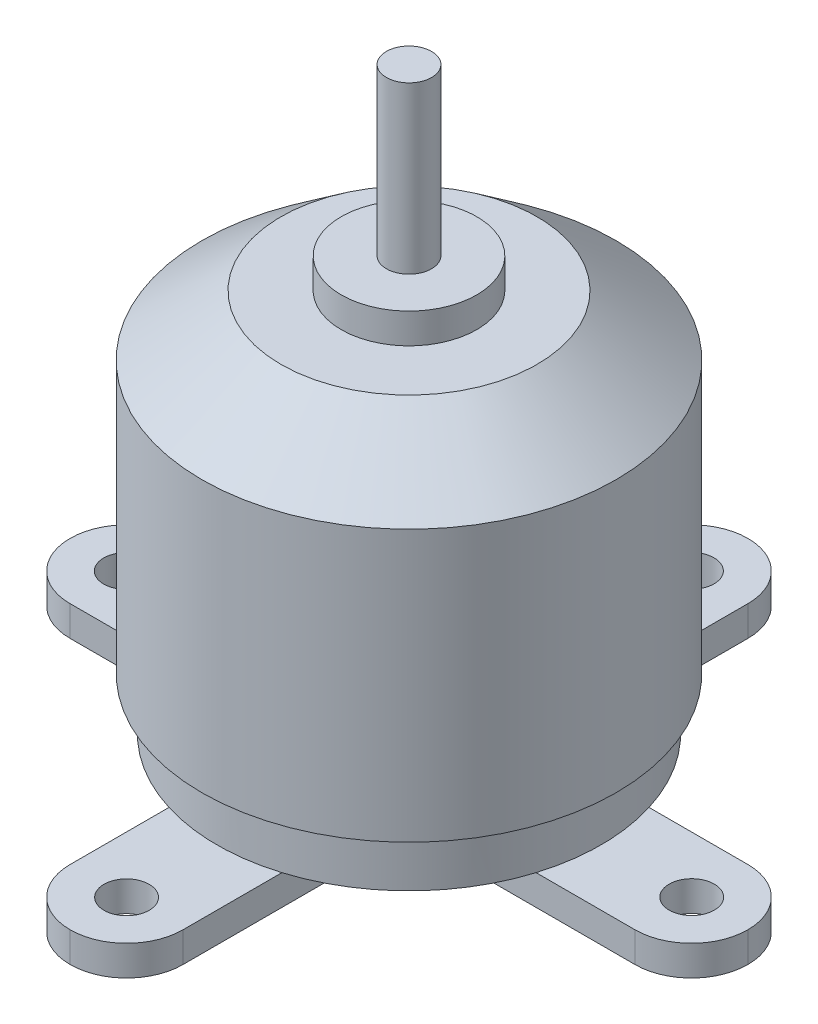
SolidWorks part; units mm, degrees
ref_plane "Alzado" through (0, 0, 0) normal (0, 0, 1) x (1, 0, 0)
ref_plane "Planta" through (0, 0, 0) normal (0, 1, 0) x (1, 0, 0)
ref_plane "Vista lateral" through (0, 0, 0) normal (1, 0, 0) x (0, 0, -1)
sketch "Croquis1" plane through (0, 0, 0) normal (0, 1, 0) x (1, 0, 0)
  circle A0 centre (0, 0) radius 13.75
  dimension "D1" = 27.5
extrude "Saliente-Extruir1" add sketch "Croquis1" along normal blind 18
sketch "Croquis3" plane through (0, 18, 0) normal (0, 1, 0) x (1, 0, 0)
  circle A0 centre (0, 0) radius 8.5
  dimension "D1" = 17
extrude "Saliente-Extruir2" add sketch "Croquis3" along normal blind 4
sketch "Croquis4" plane through (0, 22, 0) normal (0, 1, 0) x (1, 0, 0)
  circle A0 centre (0, 0) radius 4.5
  dimension "D1" = 9
extrude "Saliente-Extruir3" add sketch "Croquis4" along normal blind 2
sketch "Croquis5" plane through (0, 24, 0) normal (0, 1, 0) x (1, 0, 0)
  circle A0 centre (0, 0) radius 1.5
  dimension "D1" = 3
extrude "Saliente-Extruir4" add sketch "Croquis5" along normal blind 11
sketch "Croquis6" plane through (0, 0, 0) normal (0, 0, 1) x (1, 0, 0)
  line L0 (13.75, 18) -> (8.5, 22)
  line L1 (8.5, 22) -> (8.5, 18)
  line L2 (8.5, 18) -> (13.75, 18)
  line L3 (0, 18) -> (0, 0) construction
  line L4 (13.75, 18) -> (-13.75, 18) construction
revolve "Revolución1" add sketch "Croquis6" angle 360 about L3
sketch "Croquis7" plane through (0, 0, 0) normal (0, -1, 0) x (1, 0, 0)
  circle A0 centre (0, 0) radius 12.75
  dimension "D1" = 25.5
extrude "Saliente-Extruir5" add sketch "Croquis7" along normal blind 3.5
sketch "Croquis8" plane through (0, -3.5, 0) normal (0, -1, 0) x (1, 0, 0)
  line L0 (0, 18.9574) -> (0, -20.225) construction
  line L1 (0, 0) -> (-17.7259, 0) construction
  line L2 (7.49, 3.75) -> (18.76, 3.75)
  line L3 (0.01, 22.5) -> (-0.01, 22.5)
  line L4 (3.75, 18.76) -> (3.75, 7.49)
  line L5 (0.01, -22.5) -> (-0.01, -22.5)
  line L6 (-3.75, 18.76) -> (-3.75, 7.49)
  line L7 (3.75, 22.5) -> (-3.75, -22.5) construction
  line L8 (3.75, -22.5) -> (-3.75, 22.5) construction
  line L9 (-18.76, 3.75) -> (-7.49, 3.75)
  line L10 (-22.5, 0.01) -> (-22.5, -0.01)
  line L11 (-18.76, -3.75) -> (-7.49, -3.75)
  line L12 (22.5, 0.01) -> (22.5, -0.01)
  line L13 (-22.5, 3.75) -> (22.5, -3.75) construction
  line L14 (-22.5, -3.75) -> (22.5, 3.75) construction
  line L15 (3.75, -7.49) -> (3.75, -18.76)
  line L16 (7.49, -3.75) -> (18.76, -3.75)
  line L17 (-3.75, -7.49) -> (-3.75, -18.76)
  circle A0 centre (0, 0) radius 5
  arc A1 (3.75, -7.49) -> (7.49, -3.75) centre (7.49, -7.49) cw
  arc A2 (7.49, 3.75) -> (3.75, 7.49) centre (7.49, 7.49) cw
  arc A3 (-7.49, 3.75) -> (-3.75, 7.49) centre (-7.49, 7.49) ccw
  arc A4 (-7.49, -3.75) -> (-3.75, -7.49) centre (-7.49, -7.49) cw
  arc A5 (-22.5, -0.01) -> (-18.76, -3.75) centre (-18.76, -0.01) ccw
  arc A6 (-18.76, 3.75) -> (-22.5, 0.01) centre (-18.76, 0.01) ccw
  arc A7 (3.75, -18.76) -> (0.01, -22.5) centre (0.01, -18.76) cw
  arc A8 (-0.01, -22.5) -> (-3.75, -18.76) centre (-0.01, -18.76) cw
  arc A9 (-0.01, 22.5) -> (-3.75, 18.76) centre (-0.01, 18.76) ccw
  arc A10 (0.01, 22.5) -> (3.75, 18.76) centre (0.01, 18.76) cw
  arc A11 (18.76, 3.75) -> (22.5, 0.01) centre (18.76, 0.01) cw
  arc A12 (18.76, -3.75) -> (22.5, -0.01) centre (18.76, -0.01) ccw
  point P18 (0, 0)
  point P19 (0, 0)
  point P20 (0, 0)
  point P23 (3.75, -3.75)
  point P30 (-3.75, -3.75)
  point P55 (0, 0)
  dimension "D1" = 10
  dimension "D6" = 3.74
  dimension "D2" = 45
  dimension "D3" = 45
  dimension "D4" = 7.5
  dimension "D5" = 7.5
extrude "Saliente-Extruir6" add sketch "Croquis8" along normal blind 2
hole_wizard "Taladro de margen para M11" positions "Croquis9" profile "Croquis10" hole size "M1" standard "GB"
sketch "Croquis9" plane through (0, -5.5, 0) normal (0, -1, 0) x (-1, 0, 0)
  point P0 (0.01, 18.76)
  point P3 (-18.76, 0.01)
  point P6 (-0.01, -18.76)
  point P9 (18.76, -0.01)
sketch "Croquis10" plane through (-0.01, -5.5, -18.76) normal (1, 0, 0) x (0, 0, -1)
  line L0 (0, 0) -> (0, 5)
  line L1 (0, 5) -> (1.5, 5)
  line L2 (1.5, 5) -> (1.5, 0)
  line L5 (1.5, 0) -> (0, 0)
  line L10 (0, 5) -> (-1.5, 5) construction
  line L11 (0, -6.35) -> (0, 107.95) construction
  dimension "Diámetro de taladro" = 3
  dimension "Profundidad de taladro" = 5
  dimension "Ángulo de perforador" = 180
